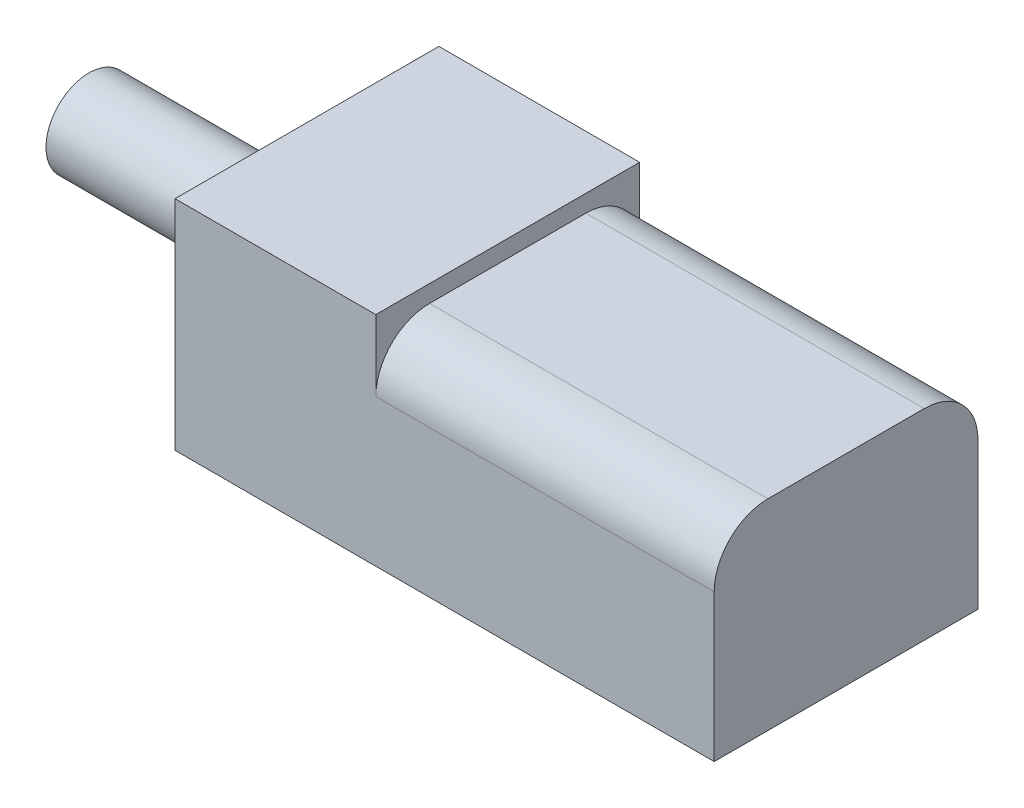
SolidWorks part; units mm, degrees
ref_plane "Front Plane" through (0, 0, 0) normal (0, 0, 1) x (1, 0, 0)
ref_plane "Top Plane" through (0, 0, 0) normal (0, 1, 0) x (1, 0, 0)
ref_plane "Right Plane" through (0, 0, 0) normal (1, 0, 0) x (0, 0, -1)
sketch "Sketch1" plane through (0, 0, 0) normal (0, 1, 0) x (1, 0, 0)
  line L1 (0, 0) -> (14.986, 0)
  line L2 (0, 0) -> (0, 11.684)
  line L3 (0, 11.684) -> (14.986, 11.684)
  line L4 (14.986, 0) -> (14.986, 11.684)
  point P7 (0, 0)
  point P8 (0, 0)
  point P9 (0, 0)
  point P10 (0, 0)
  dimension "D1" = 14.986
  dimension "D2" = 11.684
extrude "Boss-Extrude2" add sketch "Sketch1" along normal blind 8.89 contours L3 L4 L1 L2
sketch "Sketch3" plane through (0, 0, 0) normal (0, -1, 0) x (1, 0, 0)
  line L1 (0, 0) -> (-8.89, 0)
  line L2 (0, 0) -> (0, -11.684)
  line L3 (0, -11.684) -> (-8.89, -11.684)
  line L4 (-8.89, 0) -> (-8.89, -11.684)
  dimension "D1" = 11.684
  dimension "D2" = 8.89
extrude "Boss-Extrude4" add sketch "Sketch3" against normal blind 9.652
fillet "Fillet1" radius 2.38 2 edges at (7.493, 8.89, -11.684) (7.493, 8.89, 0)
sketch "Sketch4" plane through (-8.89, 0, 0) normal (-1, 0, 0) x (0, 0, 1)
  line L0 (0, 9.652) -> (-11.684, 9.652) construction
  line L1 (0, 9.652) -> (0, 0) construction
  circle A0 centre (-5.842, 4.826) radius 1.905
  point P2 (0, 0)
  point P5 (-5.842, 9.652)
  point P8 (0, 0)
  point P9 (0, 4.826)
  dimension "D1" = 3.81
extrude "Boss-Extrude5" add sketch "Sketch4" along normal blind 9.652
sketch "Sketch5" plane through (-8.89, 0, 0) normal (-1, 0, 0) x (0, 0, 1)
  line L0 (0, 9.652) -> (0, 0) construction
  line L1 (-5.842, 0) -> (-5.842, 9.652) construction
  line L2 (0, 0) -> (-11.684, 0) construction
  line L3 (0, 9.652) -> (-11.684, 9.652) construction
  circle A0 centre (-1.397, 4.826) radius 0.889
  circle A1 centre (-10.287, 4.826) radius 0.889
  point P4 (0, 4.826)
  dimension "D1" = 1.778
  dimension "D2" = 1.397
extrude "Cut-Extrude1" cut sketch "Sketch5" against normal blind 7.112
